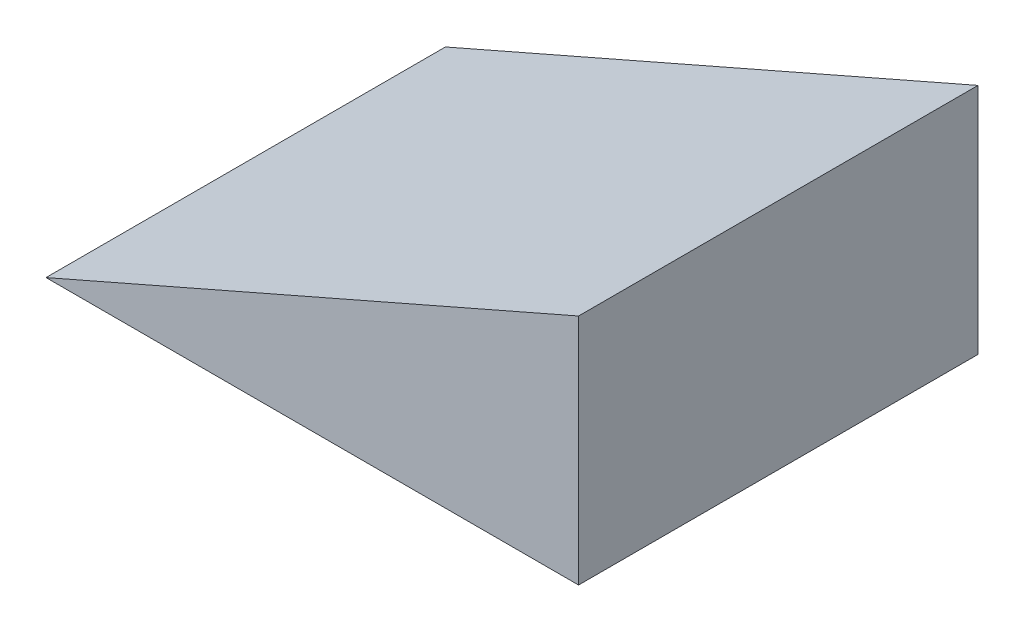
SolidWorks part; units mm, degrees
ref_plane "Front Plane" through (0, 0, 0) normal (0, 0, 1) x (1, 0, 0)
ref_plane "Top Plane" through (0, 0, 0) normal (0, 1, 0) x (1, 0, 0)
ref_plane "Right Plane" through (0, 0, 0) normal (1, 0, 0) x (0, 0, -1)
sketch "Sketch1" plane through (0, 0, 0) normal (0, 0, 1) x (1, 0, 0)
  line L0 (0, 0) -> (80, 35)
  line L1 (80, 35) -> (80, 0)
  line L2 (80, 0) -> (0, 0)
  dimension "D1" = 80
  dimension "D2" = 35
extrude "Boss-Extrude1" add sketch "Sketch1" along normal blind 60
